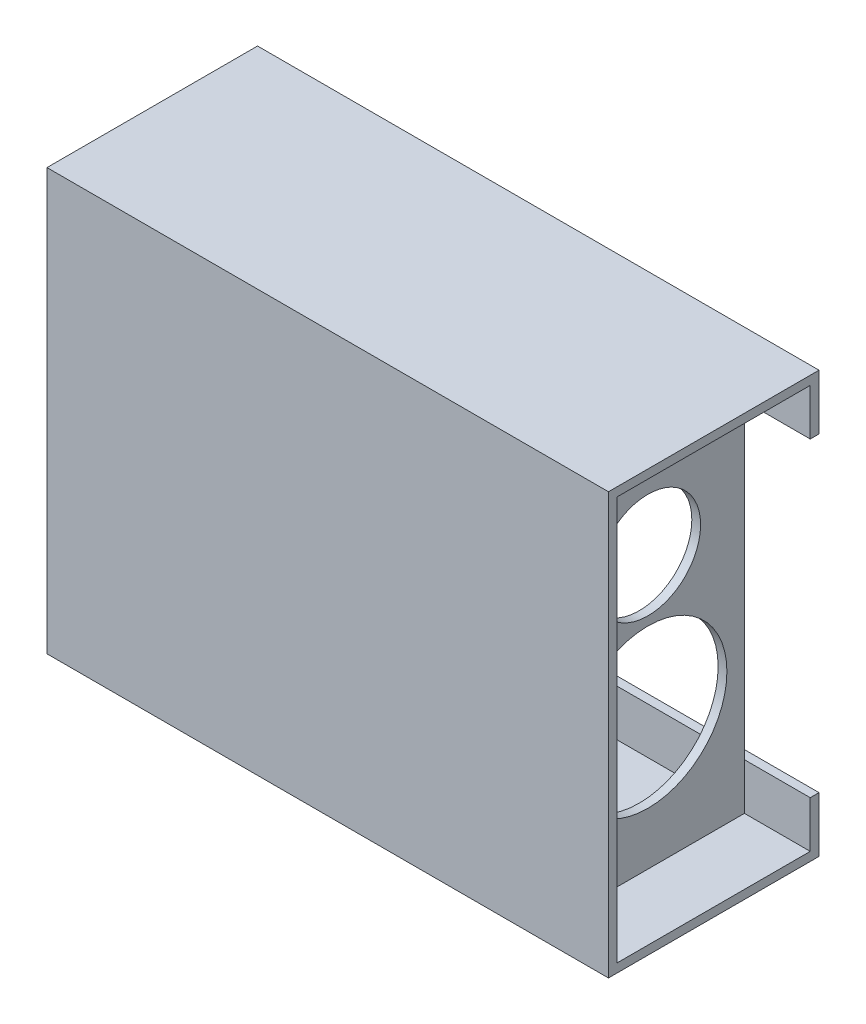
SolidWorks part; units mm, degrees
ref_plane "Front Plane" through (0, 0, 0) normal (1, 0, 0) x (0, 1, 0)
ref_plane "Top Plane" through (0, 0, 0) normal (0, 0, 1) x (0, 1, 0)
ref_plane "Right Plane" through (0, 0, 0) normal (0, 1, 0) x (-1, 0, 0)
sketch "Sketch2" plane through (0, 0, 0) normal (1, 0, 0) x (0, 1, 0)
  line L1 (-70.2342, 35.2527) -> (82.1658, 35.2527)
  line L2 (-70.2342, 35.2527) -> (-70.2342, -40.9473)
  line L3 (-70.2342, -40.9473) -> (82.1658, -40.9473)
  line L4 (82.1658, 35.2527) -> (82.1658, -40.9473)
  dimension "D1" = 76.2
  dimension "D2" = 152.4
extrude "Boss-Extrude1" add sketch "Sketch2" along normal blind 3.175
sketch "Sketch3" plane through (3.175, 0, 0) normal (1, 0, 0) x (0, 1, 0)
  line L0 (82.1658, 35.2527) -> (-70.2342, 35.2527) construction
  line L1 (-70.2342, 35.2527) -> (82.1658, 35.2527)
  line L2 (-70.2342, 35.2527) -> (-70.2342, -40.9473)
  line L3 (-70.2342, -40.9473) -> (82.1658, -40.9473)
  line L4 (82.1658, 35.2527) -> (82.1658, -40.9473)
  line L5 (82.1658, -40.9473) -> (82.1658, 35.2527) construction
  line L6 (-70.2342, -40.9473) -> (82.1658, -40.9473) construction
  line L7 (-70.2342, 35.2527) -> (-70.2342, -40.9473) construction
  line L9 (-67.0592, 32.0777) -> (78.9908, 32.0777)
  line L10 (-67.0592, 32.0777) -> (-67.0592, -37.7723)
  line L11 (-67.0592, -37.7723) -> (78.9908, -37.7723)
  line L12 (78.9908, 32.0777) -> (78.9908, -37.7723)
  dimension "D1" = 0
  dimension "D2" = 0
  dimension "D3" = 0
  dimension "D4" = 0
  dimension "D5" = 3.175
  dimension "D6" = 3.175
  dimension "D7" = 3.175
  dimension "D8" = 3.175
extrude "Boss-Extrude2" add sketch "Sketch3" along normal blind 71.4375
sketch "Sketch4" plane through (74.6125, 0, 0) normal (1, 0, 0) x (0, 1, 0)
  line L0 (82.1658, 35.2527) -> (-70.2342, 35.2527) construction
  line L1 (-70.2342, 35.2527) -> (82.1658, 35.2527)
  line L2 (-70.2342, 35.2527) -> (-70.2342, -40.9473)
  line L3 (-70.2342, -40.9473) -> (82.1658, -40.9473)
  line L4 (82.1658, 35.2527) -> (82.1658, -40.9473)
  line L5 (-70.2342, 35.2527) -> (-70.2342, -40.9473) construction
  line L6 (82.1658, -40.9473) -> (82.1658, 35.2527) construction
  line L7 (-70.2342, -40.9473) -> (82.1658, -40.9473) construction
  dimension "D1" = 0
  dimension "D2" = 0
  dimension "D3" = 0
  dimension "D4" = 0
extrude "Boss-Extrude3" add sketch "Sketch4" along normal blind 3.175
sketch "Sketch5" plane through (77.7875, 0, 0) normal (1, 0, 0) x (0, 1, 0)
  line L0 (82.1658, 35.2527) -> (-70.2342, 35.2527) construction
  line L1 (-70.2342, 35.2527) -> (82.1658, 35.2527)
  line L2 (-70.2342, 35.2527) -> (-70.2342, -40.9473)
  line L3 (-70.2342, -40.9473) -> (82.1658, -40.9473)
  line L4 (82.1658, 35.2527) -> (82.1658, -40.9473)
  line L5 (-70.2342, 35.2527) -> (-70.2342, -40.9473) construction
  line L6 (-70.2342, -40.9473) -> (82.1658, -40.9473) construction
  line L7 (82.1658, -40.9473) -> (82.1658, 35.2527) construction
  line L9 (-67.0592, 32.0777) -> (78.9908, 32.0777)
  line L10 (-67.0592, 32.0777) -> (-67.0592, -37.7723)
  line L11 (-67.0592, -37.7723) -> (78.9908, -37.7723)
  line L12 (78.9908, 32.0777) -> (78.9908, -37.7723)
  dimension "D1" = 0
  dimension "D2" = 0
  dimension "D3" = 0
  dimension "D4" = 0
  dimension "D5" = 3.175
  dimension "D6" = 3.175
  dimension "D7" = 3.175
  dimension "D8" = 3.175
extrude "Boss-Extrude4" add sketch "Sketch5" along normal blind 98.425
sketch "Sketch6" plane through (176.2125, 0, 0) normal (1, 0, 0) x (0, 1, 0)
  line L0 (82.1658, 35.2527) -> (-70.2342, 35.2527) construction
  line L1 (-70.2342, 35.2527) -> (82.1658, 35.2527)
  line L2 (-70.2342, 35.2527) -> (-70.2342, -40.9473)
  line L3 (-70.2342, -40.9473) -> (82.1658, -40.9473)
  line L4 (82.1658, 35.2527) -> (82.1658, -40.9473)
  line L5 (-70.2342, 35.2527) -> (-70.2342, -40.9473) construction
  line L6 (-70.2342, -40.9473) -> (82.1658, -40.9473) construction
  line L7 (82.1658, -40.9473) -> (82.1658, 35.2527) construction
  dimension "D1" = 0
  dimension "D2" = 0
  dimension "D3" = 0
  dimension "D4" = 0
hole_wizard "#97 (1) Diameter Hole1" positions "Sketch7" profile "Sketch9" hole size "#97" standard "ANSI Inch" end condition through all
sketch "Sketch7" plane through (77.7875, 0, 0) normal (1, 0, 0) x (0, 1, 0)
  line L0 (-70.2342, -40.9473) -> (82.1658, -40.9473) construction
  line L1 (82.1658, 35.2527) -> (82.1658, -40.9473) construction
  line L2 (-70.2342, 35.2527) -> (-70.2342, -40.9473) construction
  point P0 (-19.4342, -2.8473)
  point P2 (31.3658, -2.8473)
  dimension "D1" = 38.1
  dimension "D2" = 50.8
  dimension "D3" = 38.1
  dimension "D4" = 50.8
sketch "Sketch9" plane through (77.7875, -19.4342, -2.8473) normal (0, 1, 0) x (0, 0, -1)
  line L0 (0, 0) -> (0, 77.7875)
  line L1 (0, 77.7875) -> (12.7, 77.7875)
  line L2 (12.7, 77.7875) -> (12.7, 0)
  line L5 (12.7, 0) -> (0, 0)
  line L11 (0, -6.35) -> (0, 107.95) construction
  dimension "Thru Hole Dia." = 25.4
  dimension "Thru Hole Depth" = 77.7875
hole_wizard "#97 (1.5) Diameter Hole1" positions "Sketch10" profile "Sketch11" hole size "#97" standard "ANSI Inch"
sketch "Sketch10" plane through (0, 0, 0) normal (-1, 0, 0) x (0, -1, 0)
  line L0 (-82.1658, 35.2527) -> (-82.1658, -40.9473) construction
  line L1 (70.2342, -40.9473) -> (-82.1658, -40.9473) construction
  point P0 (-31.3658, -2.8473)
  dimension "D1" = 50.8
  dimension "D2" = 38.1
sketch "Sketch11" plane through (0, 31.3658, -2.8473) normal (0, 1, 0) x (0, 0, 1)
  line L0 (0, 0) -> (0, 6.35)
  line L1 (0, 6.35) -> (19.05, 6.35)
  line L2 (19.05, 6.35) -> (19.05, 0)
  line L5 (19.05, 0) -> (0, 0)
  line L10 (0, 6.35) -> (-19.05, 6.35) construction
  line L11 (0, -6.35) -> (0, 107.95) construction
  dimension "Hole Dia." = 38.1
  dimension "Hole Depth" = 6.35
  dimension "Drill Angle" = 180
extrude "Boss-Extrude6" add sketch "Sketch6" along normal blind 3.175
hole_wizard "#97 (1.5) Diameter Hole2" positions "Sketch12" profile "Sketch13" hole size "#97" standard "ANSI Inch"
sketch "Sketch12" plane through (179.3875, 0, 0) normal (1, 0, 0) x (0, 1, 0)
  line L0 (82.1658, -40.9473) -> (82.1658, 35.2527) construction
  line L1 (-70.2342, -40.9473) -> (82.1658, -40.9473) construction
  point P0 (31.3658, -2.8473)
  dimension "D1" = 50.8
  dimension "D2" = 38.1
sketch "Sketch13" plane through (179.3875, 31.3658, -2.8473) normal (0, 1, 0) x (0, 0, -1)
  line L0 (0, 0) -> (0, 6.35)
  line L1 (0, 6.35) -> (19.05, 6.35)
  line L2 (19.05, 6.35) -> (19.05, 0)
  line L5 (19.05, 0) -> (0, 0)
  line L10 (0, 6.35) -> (-19.05, 6.35) construction
  line L11 (0, -6.35) -> (0, 107.95) construction
  dimension "Hole Dia." = 38.1
  dimension "Hole Depth" = 6.35
  dimension "Drill Angle" = 180
hole_wizard "#97 (2.25) Diameter Hole1" positions "Sketch14" profile "Sketch15" hole size "#97" standard "ANSI Inch"
sketch "Sketch14" plane through (179.3875, 0, 0) normal (1, 0, 0) x (0, 1, 0)
  line L0 (-70.2342, 35.2527) -> (-70.2342, -40.9473) construction
  line L1 (82.1658, 35.2527) -> (-70.2342, 35.2527) construction
  point P0 (-19.4342, -2.8473)
  dimension "D1" = 50.8
  dimension "D2" = 38.1
sketch "Sketch15" plane through (179.3875, -19.4342, -2.8473) normal (0, 1, 0) x (0, 0, -1)
  line L0 (0, 0) -> (0, 6.35)
  line L1 (0, 6.35) -> (28.575, 6.35)
  line L2 (28.575, 6.35) -> (28.575, 0)
  line L5 (28.575, 0) -> (0, 0)
  line L10 (0, 6.35) -> (-28.575, 6.35) construction
  line L11 (0, -6.35) -> (0, 107.95) construction
  dimension "Hole Dia." = 57.15
  dimension "Hole Depth" = 6.35
  dimension "Drill Angle" = 180
sketch "Sketch16" plane through (179.3875, 0, 0) normal (1, 0, 0) x (0, 1, 0)
  line L0 (82.1658, 35.2527) -> (-70.2342, 35.2527) construction
  line L1 (-70.2342, 35.2527) -> (82.1658, 35.2527)
  line L2 (-70.2342, 35.2527) -> (-70.2342, -40.9473)
  line L3 (-70.2342, -40.9473) -> (82.1658, -40.9473)
  line L4 (82.1658, 35.2527) -> (82.1658, -40.9473)
  line L5 (-70.2342, -40.9473) -> (82.1658, -40.9473) construction
  line L6 (-70.2342, 35.2527) -> (-70.2342, -40.9473) construction
  line L7 (82.1658, -40.9473) -> (82.1658, 35.2527) construction
  line L9 (-67.0592, 32.0777) -> (78.9908, 32.0777)
  line L10 (-67.0592, 32.0777) -> (-67.0592, -37.7723)
  line L11 (-67.0592, -37.7723) -> (78.9908, -37.7723)
  line L12 (78.9908, 32.0777) -> (78.9908, -37.7723)
  dimension "D1" = 0
  dimension "D2" = 0
  dimension "D3" = 0
  dimension "D4" = 0
  dimension "D5" = 3.175
  dimension "D6" = 3.175
  dimension "D7" = 3.175
  dimension "D8" = 3.175
extrude "Boss-Extrude7" add sketch "Sketch16" along normal blind 23.8125
sketch "Sketch17" plane through (0, 0, -40.9473) normal (0, 0, -1) x (1, 0, 0)
  line L0 (203.2, 50.2342) -> (15, 50.2342)
  line L1 (203.2, 70.2342) -> (203.2, -82.1658) construction
  line L2 (15, 50.2342) -> (15, -62.1658)
  line L3 (15, -62.1658) -> (203.2, -62.1658)
  line L4 (203.2, -62.1658) -> (203.2, 50.2342)
  line L5 (203.2, 70.2342) -> (0, 70.2342) construction
  line L6 (203.2, -82.1658) -> (0, -82.1658) construction
  line L7 (0, 70.2342) -> (0, -82.1658) construction
  dimension "D1" = 20
  dimension "D2" = 20
  dimension "D3" = 15
extrude "Cut-Extrude1" cut sketch "Sketch17" against normal up to vertex (3.175 mm away)
